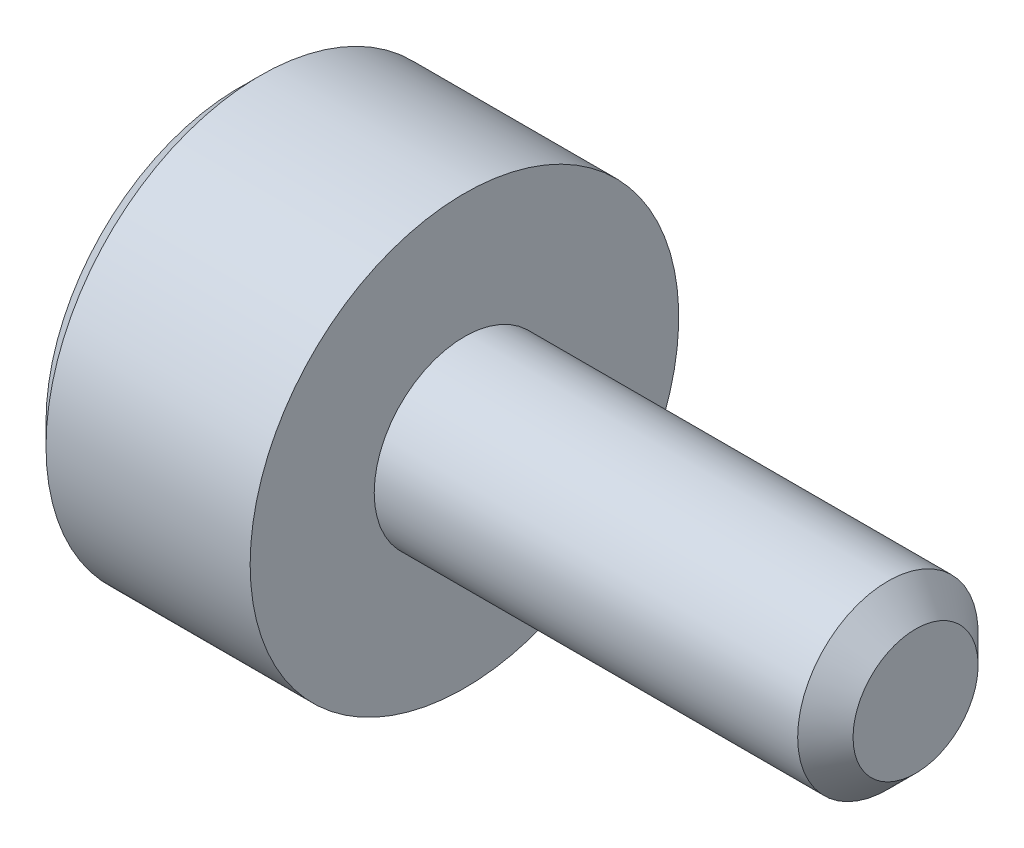
SolidWorks part; units mm, degrees
material "AISI 304"
ref_plane "正面" through (0, 0, 0) normal (0, 0, 1) x (1, 0, 0)
ref_plane "平面" through (0, 0, 0) normal (0, 1, 0) x (1, 0, 0)
ref_plane "右側面" through (0, 0, 0) normal (1, 0, 0) x (0, 0, -1)
ref_plane "Plane1" through (0, 0, 0) normal (0, 0, 1) x (1, 0, 0)
sketch "Sketch1" plane through (0, 0, 0) normal (0, 0, 1) x (1, 0, 0)
  line L0 (-2, 0) -> (-2, 1.71)
  line L1 (-2, 1.71) -> (-1.81, 1.9)
  line L2 (-1.81, 1.9) -> (0, 1.9)
  line L3 (0, 1.9) -> (0, 0.8)
  line L4 (0, 0.8) -> (3.7545, 0.8)
  line L5 (3.7545, 0.8) -> (4, 0.5545)
  line L6 (4, 0.5545) -> (4, 0)
  line L7 (4, 0) -> (-2, 0)
  line L8 (4, 0) -> (-2, 0) construction
  dimension "D1" = 0.8
revolve "Revolve1" add sketch "Sketch1" angle 360 about L8
cosmetic thread "Cosmetic Thread1" parameters "D1"=3.5748, "D2"=1.509
ref_plane "Plane2" through (-2, 0, 0) normal (1, 0, 0) x (0, 0, -1)
sketch "Sketch2" plane through (-2, 0, 0) normal (1, 0, 0) x (0, 0, -1)
  line L0 (-0.75, -0.433) -> (0, -0.866)
  line L1 (0, -0.866) -> (0.75, -0.433)
  line L2 (0.75, -0.433) -> (0.75, 0.433)
  line L3 (0.75, 0.433) -> (0, 0.866)
  line L4 (0, 0.866) -> (-0.75, 0.433)
  line L5 (-0.75, 0.433) -> (-0.75, -0.433)
extrude "Cut-Extrude1" cut sketch "Sketch2" along normal blind 0.8
